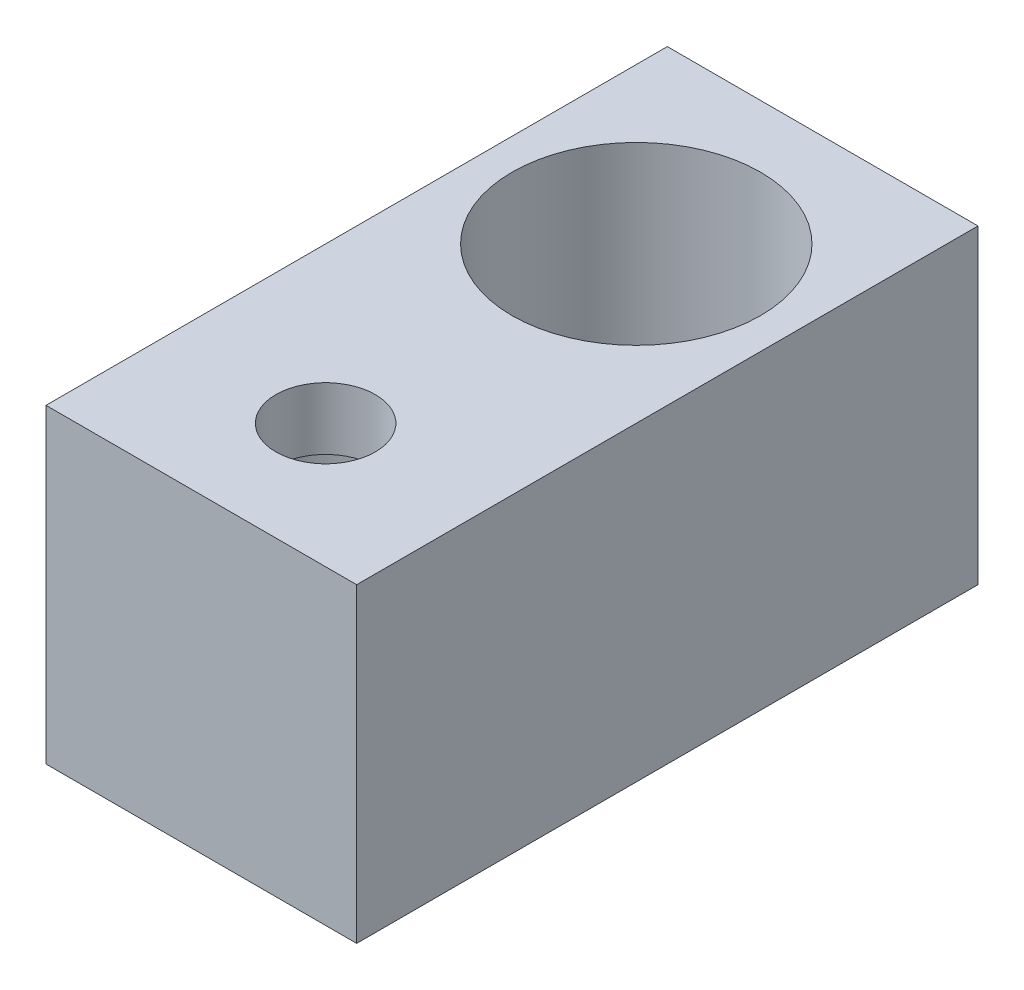
SolidWorks part; units mm, degrees
ref_plane "Front Plane" through (0, 0, 0) normal (0, 0, 1) x (1, 0, 0)
ref_plane "Top Plane" through (0, 0, 0) normal (0, 1, 0) x (1, 0, 0)
ref_plane "Right Plane" through (0, 0, 0) normal (1, 0, 0) x (0, 0, -1)
sketch "Sketch1" plane through (0, 0, 0) normal (0, 1, 0) x (1, 0, 0)
  line L1 (0, 0) -> (10, 0)
  line L2 (0, 0) -> (0, -20)
  line L3 (0, -20) -> (10, -20)
  line L4 (10, 0) -> (10, -20)
  circle A0 centre (5, -6) radius 4
  circle A1 centre (5, -16) radius 1.6
  dimension "D2" = 8
  dimension "D5" = 3.2
  dimension "D1" = 10
  dimension "D3" = 6
  dimension "D4" = 5
  dimension "D6" = 5
  dimension "D7" = 10
  dimension "D8" = 20
extrude "Boss-Extrude1" add sketch "Sketch1" along normal blind 10
sketch "Sketch2" plane through (0, 0, 0) normal (0, -1, 0) x (1, 0, 0)
  circle A0 centre (5, 16) radius 3
  dimension "D1" = 6
extrude "Cut-Extrude1" cut sketch "Sketch2" against normal blind 8
